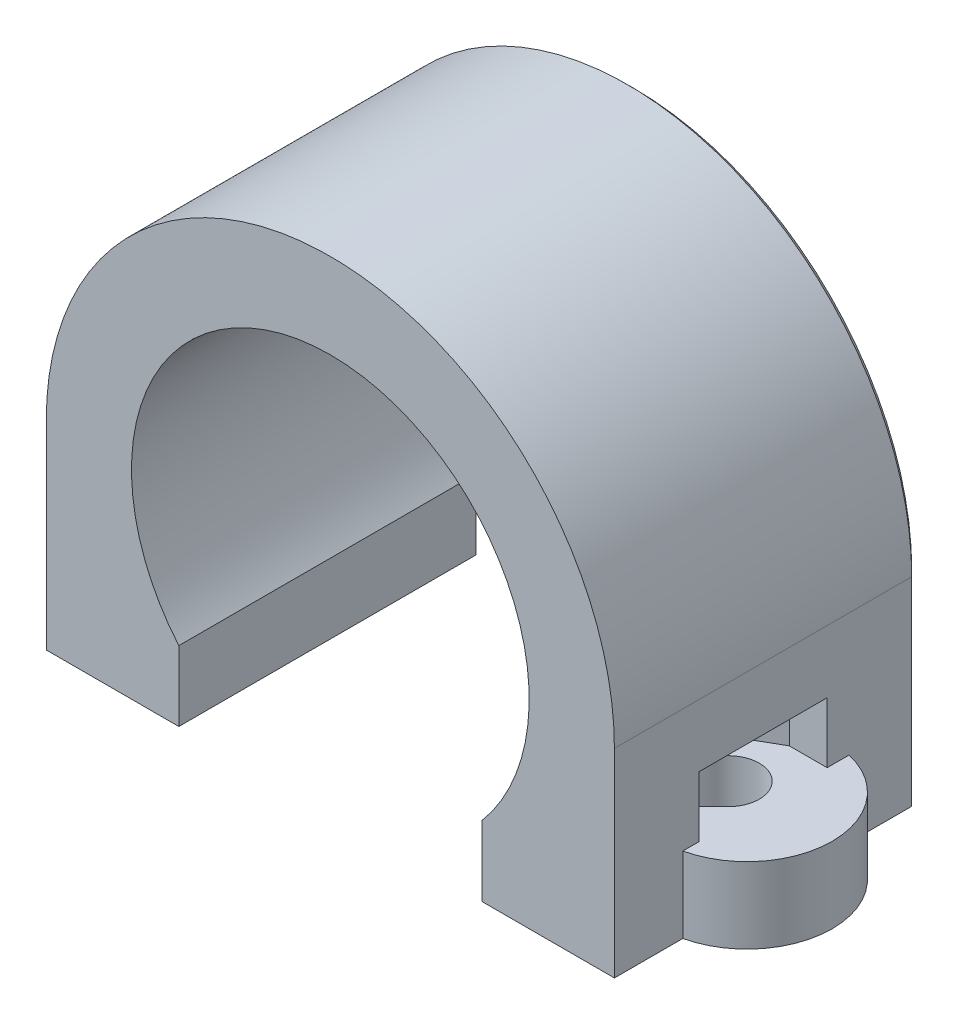
SolidWorks part; units mm, degrees
material "Custom Plastic"
ref_plane "Front Plane" through (0, 0, 0) normal (0, 0, 1) x (1, 0, 0)
ref_plane "Top Plane" through (0, 0, 0) normal (0, 1, 0) x (1, 0, 0)
ref_plane "Right Plane" through (0, 0, 0) normal (1, 0, 0) x (0, 0, -1)
sketch "Sketch1" plane through (0, 0, 0) normal (0, 0, 1) x (1, 0, 0)
  line L0 (-23.622, -10.5) -> (30.4823, -10.5) construction
  line L1 (-23.622, -16.5) -> (30.4823, -16.5) construction
  line L2 (8, -6.8007) -> (8, -10.5)
  line L3 (8, -10.5) -> (15, -10.5)
  line L4 (-15, -10.5) -> (-8, -10.5)
  line L5 (-8, -6.8007) -> (-8, -10.5)
  line L6 (15, 0) -> (15, -10.5)
  line L12 (-15, -10.5) -> (-15, 0)
  arc A4 (8, -6.8007) -> (-8, -6.8007) centre (0, 0) ccw
  arc A5 (15, 0) -> (-15, 0) centre (0, 0) ccw
  dimension "D1" = 16
  dimension "D6" = 21
  dimension "D7" = 4.5
  dimension "D2" = 6
extrude "Boss-Extrude1" add sketch "Sketch1" along normal blind 16
sketch "Sketch4" plane through (0, -10.5, 0) normal (0, -1, 0) x (1, 0, 0)
  line L0 (14, 8) -> (15, 8) construction
  line L1 (15, 16) -> (15, 0) construction
  circle A0 centre (14, 8) radius 4.5
  dimension "D1" = 9
  dimension "D2" = 1
extrude "Boss-Extrude2" add sketch "Sketch4" against normal blind 4
sketch "Sketch2" plane through (0, -10.5, 0) normal (0, -1, 0) x (1, 0, 0)
  line L0 (13, 16) -> (13, 0) construction
  line L3 (14, 8) -> (13, 8) construction
  circle A0 centre (13, 8) radius 1.65
  arc A2 (15, 3.6125) -> (15, 12.3875) centre (14, 8) ccw construction
  dimension "D1" = 3.3
  dimension "D2" = 1
extrude "Cut-Extrude1" cut sketch "Sketch2" against normal blind 10
sketch "Sketch3" plane through (0, -10.5, 0) normal (0, -1, 0) x (1, 0, 0)
  line L0 (10.2, 9.6166) -> (10.2, 9.9166)
  line L1 (13, 11.2332) -> (10.2, 9.6166) construction
  line L2 (10.2, 9.6166) -> (10.2, 6.3834)
  line L3 (10.2, 6.3834) -> (13, 4.7668)
  line L4 (13, 4.7668) -> (15.8, 6.3834) construction
  line L5 (15.8, 6.3834) -> (15.8, 9.6166) construction
  line L6 (15.8, 9.6166) -> (13, 11.2332) construction
  line L7 (13, 11.2332) -> (17.758, 11.2332) construction
  line L8 (10.2, 9.9166) -> (13, 11.5332)
  line L9 (17.758, 11.2332) -> (17.758, 4.7668)
  line L10 (17.758, 4.7668) -> (13, 4.7668)
  line L11 (13, 11.5332) -> (17.758, 11.5332)
  line L12 (17.758, 11.5332) -> (17.758, 11.2332)
  circle A0 centre (13, 8) radius 2.8 construction
  dimension "D1" = 5.6
  dimension "D2" = 0.3
extrude "Cut-Extrude2" cut sketch "Sketch3" against normal blind 3.2 from offset 4 offset against normal yes
mirror "Mirror1" about plane through (0, 0, 0) normal (1, 0, 0) of "Boss-Extrude2", "Cut-Extrude2", "Cut-Extrude1"
chamfer "Chamfer1" distance 0.3 angle 45 8 edges at (-15, -5.25, 0) (-11.5, -10.5, 0) (-8, -8.6504, 0) (0, 10.5, 0) (8, -8.6504, 0) (11.5, -10.5, 0) (15, -5.25, 0) (0, 15, 0)
sketch "Sketch5" plane through (0, -10.5, 0) normal (0, -1, 0) x (1, 0, 0)
  line L0 (-13, 8) -> (-11.8333, 9.1667)
  line L1 (-11.8333, 9.1667) -> (-12.6365, 9.97)
  line L2 (-12.6365, 9.97) -> (-13.3635, 9.97)
  line L3 (-13.3635, 9.97) -> (-14.1667, 9.1667)
  line L4 (-14.1667, 9.1667) -> (-13, 8)
  line L5 (13, 8) -> (14.1667, 9.1667)
  line L6 (14.1667, 9.1667) -> (13.3635, 9.97)
  line L7 (13.3635, 9.97) -> (12.6365, 9.97)
  line L8 (12.6365, 9.97) -> (11.8333, 9.1667)
  line L9 (11.8333, 9.1667) -> (13, 8)
  circle A0 centre (-13, 8) radius 1.65 construction
  circle A1 centre (-13, 8) radius 1.65 construction
  circle A2 centre (13, 8) radius 1.65 construction
  circle A3 centre (13, 8) radius 1.65 construction
  point P0 (-13, 9.65)
  point P11 (13, 9.65)
  dimension "D1" = 0.32
  dimension "D2" = 0.32
extrude "Cut-Extrude3" cut sketch "Sketch5" against normal up to surface (10 mm away) up to face at (-13, -0.5, 6.35)
equation "\"y-cross-rib-thickness\"=6"
equation "\"y-rib-thickness\"=6"
equation "\"bed-plate-thickness\"=6"
equation "\"x-plate-thickness\"=5"
equation "\"rod-diameter\"=12"
equation "\"t-nut-hole-diameter\"=3"
equation "\"y-plate-thickness\"=5"
equation "\"enclosure-thickness\"=0.6"
equation "\"M3-Clearance\"=3.3"
equation "\"M4-Clearance\"=4.3"
equation "\"M5-Clearance\"=5.3"
equation "\"M6-Clearance\"=6.3"
equation "\"M8-Clearance\"=8.3"
equation "\"623-Bearing-Dia\"=11.2"
